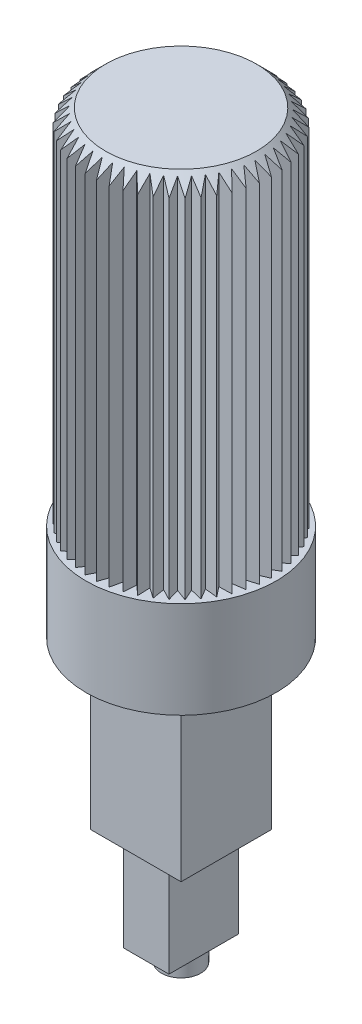
SolidWorks part; units mm, degrees
ref_plane "Спереди" through (0, 0, 0) normal (0, 0, 1) x (1, 0, 0)
ref_plane "Сверху" through (0, 0, 0) normal (0, 1, 0) x (1, 0, 0)
ref_plane "Справа" through (0, 0, 0) normal (1, 0, 0) x (0, 0, -1)
sketch "Эскиз1" plane through (0, 0, 0) normal (0, 1, 0) x (1, 0, 0)
  circle A0 centre (0, 0) radius 3.15
  dimension "D1" = 6.3
extrude "Бобышка-Вытянуть1" add sketch "Эскиз1" along normal blind 3.2
sketch "Эскиз2" plane through (0, 3.2, 0) normal (0, 1, 0) x (1, 0, 0)
  circle A0 centre (0, 0) radius 3
  dimension "D1" = 6
extrude "Бобышка-Вытянуть2" add sketch "Эскиз2" along normal blind 12
chamfer "Фаска1" distance 0.5 angle 45 1 edges at (0, 15.2, 3)
sketch "Эскиз3" plane through (0, 0, 0) normal (0, -1, 0) x (1, 0, 0)
  line L1 (-1.5, 1.5) -> (1.5, 1.5)
  line L2 (-1.5, 1.5) -> (-1.5, -1.5)
  line L3 (-1.5, -1.5) -> (1.5, -1.5)
  line L4 (1.5, 1.5) -> (1.5, -1.5)
  line L5 (-1.5, 1.5) -> (1.5, -1.5) construction
  line L6 (-1.5, -1.5) -> (1.5, 1.5) construction
  point P0 (0, 0)
  dimension "D1" = 3
  dimension "D2" = 3
extrude "Бобышка-Вытянуть3" add sketch "Эскиз3" along normal blind 5.5
sketch "Эскиз4" plane through (0, -5.5, 0) normal (0, -1, 0) x (1, 0, 0)
  line L1 (-0.75, 1.15) -> (0.75, 1.15)
  line L2 (-0.75, 1.15) -> (-0.75, -1.15)
  line L3 (-0.75, -1.15) -> (0.75, -1.15)
  line L4 (0.75, 1.15) -> (0.75, -1.15)
  line L5 (-0.75, 1.15) -> (0.75, -1.15) construction
  line L6 (-0.75, -1.15) -> (0.75, 1.15) construction
  point P0 (0, 0)
  dimension "D1" = 2.3
  dimension "D2" = 1.5
extrude "Бобышка-Вытянуть4" add sketch "Эскиз4" along normal blind 3.2
sketch "Эскиз5" plane through (0, -8.7, 0) normal (0, -1, 0) x (1, 0, 0)
  circle A0 centre (0, 0) radius 0.65
  dimension "D1" = 1.3
extrude "Бобышка-Вытянуть5" add sketch "Эскиз5" along normal blind 0.6
sketch "Эскиз7" plane through (0, 15.2, 0) normal (0, 1, 0) x (1, 0, 0)
  line L0 (0, 2.6122) -> (-0.2, 3.0122)
  line L1 (-0.2, 3.0122) -> (0.2, 3.0122)
  line L2 (0.2, 3.0122) -> (0, 2.6122)
  point P2 (0, 3.0122)
  point P4 (0, 0)
  dimension "D1" = 0.4
  dimension "D2" = 0.4
extrude "Вырез-Вытянуть1" cut sketch "Эскиз7" against normal blind 12
pattern_circular "Круговой массив1" count 50 over 360 about axis through (0, 0, 0) along (0, 1, 0) of "Вырез-Вытянуть1"
